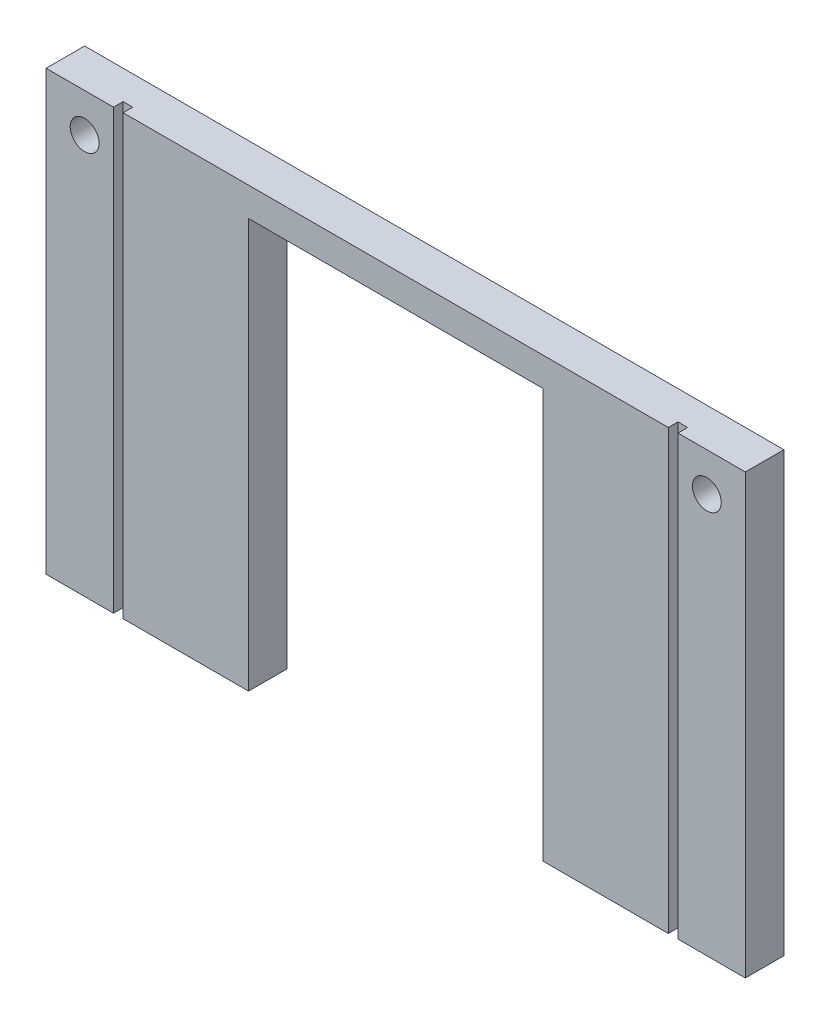
SolidWorks part; units mm, degrees
ref_plane "Front Plane" through (0, 0, 0) normal (0, 0, 1) x (1, 0, 0)
ref_plane "Top Plane" through (0, 0, 0) normal (0, 1, 0) x (1, 0, 0)
ref_plane "Right Plane" through (0, 0, 0) normal (1, 0, 0) x (0, 0, -1)
sketch "Sketch1" plane through (0, 0, 0) normal (0, 0, 1) x (1, 0, 0)
  line L0 (0, 0) -> (72.6, 0)
  line L1 (72.6, 0) -> (72.6, 45.5)
  line L2 (72.6, 45.5) -> (0, 45.5)
  line L3 (0, 45.5) -> (0, 0)
  circle A0 centre (4, 41.5) radius 1.5
  circle A1 centre (68.6, 41.5) radius 1.5
  dimension "D1" = 3
  dimension "D2" = 3
  dimension "D3" = 72.6
  dimension "D4" = 45.5
  dimension "D5" = 4
  dimension "D6" = 4
  dimension "D7" = 4
extrude "Boss-Extrude1" add sketch "Sketch1" along normal blind 4
sketch "Sketch2" plane through (0, 0, 4) normal (0, 0, 1) x (1, 0, 0)
  line L0 (36.3, 45.5) -> (36.3, 0) construction
  line L1 (72.6, 45.5) -> (0, 45.5) construction
  line L2 (0, 0) -> (72.6, 0) construction
  line L3 (7, 45.5) -> (7, 0)
  line L4 (7, 0) -> (8, 0)
  line L5 (8, 0) -> (8, 45.5)
  line L6 (8, 45.5) -> (7, 45.5)
  line L7 (64.6, 0) -> (64.6, 45.5)
  line L8 (65.6, 0) -> (64.6, 0)
  line L9 (65.6, 45.5) -> (65.6, 0)
  line L10 (64.6, 45.5) -> (65.6, 45.5)
  dimension "D1" = 1
  dimension "D2" = 56.6
extrude "Cut-Extrude1" cut sketch "Sketch2" against normal blind 1
sketch "Sketch3" plane through (0, 0, 4) normal (0, 0, 1) x (1, 0, 0)
  line L0 (21.0125, 0) -> (21.0125, 42.5)
  line L1 (8, 0) -> (64.6, 0) construction
  line L2 (21.0125, 42.5) -> (51.5875, 42.5)
  line L3 (51.5875, 42.5) -> (51.5875, 0)
  line L4 (51.5875, 0) -> (21.0125, 0)
  line L7 (64.6, 45.5) -> (8, 45.5) construction
  point P8 (36.3, 45.5)
  point P9 (36.3, 42.5)
  dimension "D1" = 30.575
  dimension "D3" = 42.5
extrude "Cut-Extrude2" cut sketch "Sketch3" against normal up to surface (4 mm away) up to face at (36.3, 22.75, 0)
equation "\"D6@Sketch1\"=\"D5@Sketch1\""
